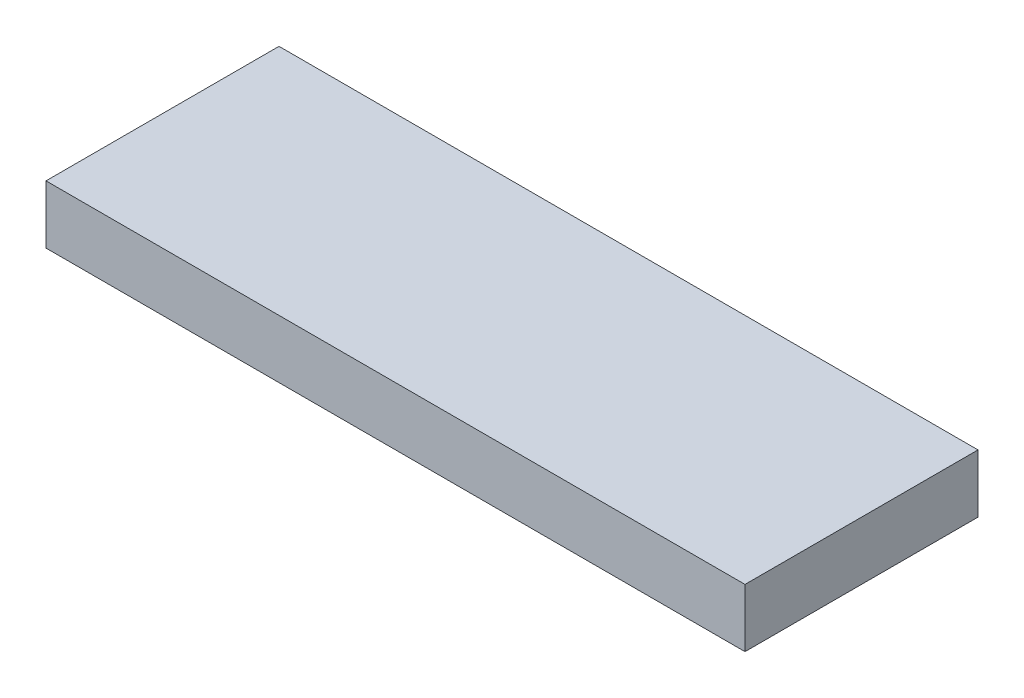
SolidWorks part; units mm, degrees
ref_plane "Front Plane" through (0, 0, 0) normal (0, 0, 1) x (1, 0, 0)
ref_plane "Top Plane" through (0, 0, 0) normal (0, 1, 0) x (1, 0, 0)
ref_plane "Right Plane" through (0, 0, 0) normal (1, 0, 0) x (0, 0, -1)
sketch "Sketch1" plane through (0, 0, 0) normal (0, 1, 0) x (1, 0, 0)
  line L1 (0, 0) -> (76.2, 0)
  line L2 (0, 0) -> (0, 25.4)
  line L3 (0, 25.4) -> (76.2, 25.4)
  line L4 (76.2, 0) -> (76.2, 25.4)
  dimension "D1" = 25.4
  dimension "D2" = 76.2
extrude "Boss-Extrude1" add sketch "Sketch1" along normal blind 6.35
